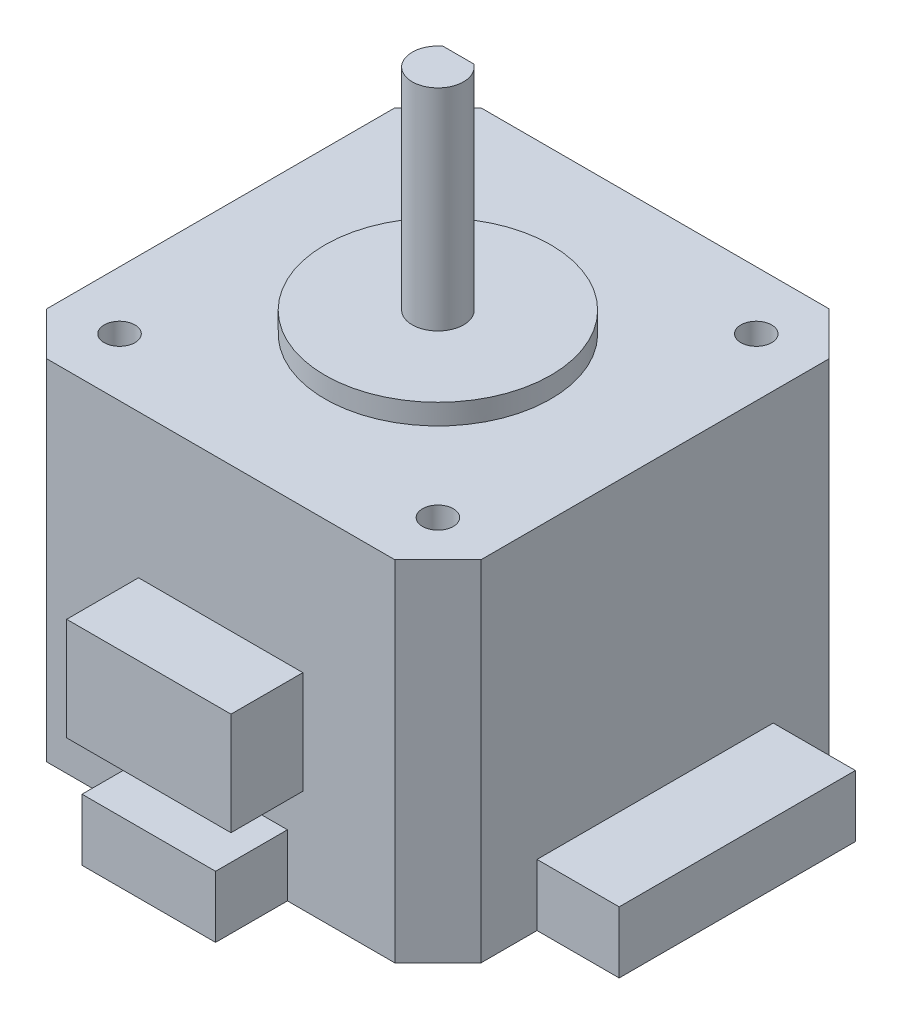
SolidWorks part; units mm, degrees
ref_plane "前视基准面" through (0, 0, 0) normal (0, 0, 1) x (1, 0, 0)
ref_plane "上视基准面" through (0, 0, 0) normal (0, 1, 0) x (1, 0, 0)
ref_plane "右视基准面" through (0, 0, 0) normal (1, 0, 0) x (0, 0, -1)
other "Configuration Table"
sketch "草图1" plane through (0, 0, 0) normal (0, 1, 0) x (1, 0, 0)
  line L1 (0, 0) -> (42.3, 0)
  line L2 (0, 0) -> (0, 42.3)
  line L3 (0, 42.3) -> (42.3, 42.3)
  line L4 (42.3, 0) -> (42.3, 42.3)
  dimension "D1" = 42.3
  dimension "D2" = 42.3
extrude "凸台-拉伸1" add sketch "草图1" along normal blind 34
chamfer "倒角1" distance 4.2 angle 45 4 edges at (0, 17, -42.3) (42.3, 17, -42.3) (0, 17, 0) (42.3, 17, 0)
sketch "草图2" plane through (0, 34, 0) normal (0, 1, 0) x (1, 0, 0)
  line L0 (0, 21.15) -> (42.3, 21.15) construction
  line L1 (0, 38.1) -> (0, 4.2) construction
  line L2 (42.3, 4.2) -> (42.3, 38.1) construction
  line L3 (21.15, 42.3) -> (21.15, 0) construction
  line L4 (38.1, 42.3) -> (4.2, 42.3) construction
  line L5 (4.2, 0) -> (38.1, 0) construction
  circle A0 centre (5.65, 36.65) radius 1.5
  circle A1 centre (36.65, 36.65) radius 1.5
  circle A2 centre (5.65, 5.65) radius 1.5
  circle A3 centre (36.65, 5.65) radius 1.5
  dimension "D1" = 31
  dimension "D2" = 31
  dimension "D3" = 3
extrude "切除-拉伸1" cut sketch "草图2" against normal blind 4.5
sketch "草图3" plane through (0, 34, 0) normal (0, 1, 0) x (1, 0, 0)
  line L0 (0, 21.15) -> (42.3, 21.15) construction
  line L1 (0, 38.1) -> (0, 4.2) construction
  line L2 (42.3, 4.2) -> (42.3, 38.1) construction
  circle A0 centre (21.15, 21.15) radius 11
  point P2 (21.15, 21.15)
  dimension "D1" = 22
extrude "凸台-拉伸2" add sketch "草图3" along normal blind 2
sketch "草图4" plane through (0, 36, 0) normal (0, 1, 0) x (1, 0, 0)
  circle A0 centre (21.15, 21.15) radius 2.5
  dimension "D1" = 5
extrude "凸台-拉伸3" add sketch "草图4" along normal blind 20.5
sketch "草图5" plane through (0, 56.5, 0) normal (0, 1, 0) x (1, 0, 0)
  line L0 (19.65, 23.15) -> (22.65, 23.15)
  circle A0 centre (21.15, 21.15) radius 2.5 construction
  arc A1 (22.65, 23.15) -> (19.65, 23.15) centre (21.15, 21.15) ccw
  dimension "D1" = 2
extrude "切除-拉伸2" cut sketch "草图5" against normal blind 18
sketch "草图6" plane through (0, 0, 0) normal (0, 0, 1) x (1, 0, 0)
  line L0 (21.15, 34) -> (21.15, 0) construction
  line L1 (4.2, 34) -> (38.1, 34) construction
  line L2 (4.2, 0) -> (38.1, 0) construction
  line L4 (13.15, 20) -> (29.15, 20)
  line L5 (13.15, 20) -> (13.15, 10)
  line L6 (13.15, 10) -> (29.15, 10)
  line L7 (29.15, 20) -> (29.15, 10)
  line L8 (14.65, 0) -> (27.65, 0)
  line L9 (14.65, 0) -> (14.65, 6)
  line L10 (14.65, 6) -> (27.65, 6)
  line L11 (27.65, 0) -> (27.65, 6)
  point P10 (0, 0)
  dimension "D1" = 16
  dimension "D2" = 10
  dimension "D3" = 24
  dimension "D4" = 13
  dimension "D5" = 6
extrude "凸台-拉伸4" add sketch "草图6" along normal blind 7
sketch "草图7" plane through (42.3, 0, 0) normal (1, 0, 0) x (0, 0, -1)
  line L0 (4.2, 0) -> (38.1, 0) construction
  line L1 (9.65, 0) -> (32.65, 0)
  line L2 (9.65, 0) -> (9.65, 6)
  line L3 (9.65, 6) -> (32.65, 6)
  line L4 (32.65, 0) -> (32.65, 6)
  line L5 (21.15, 34) -> (21.15, 0) construction
  line L6 (4.2, 34) -> (38.1, 34) construction
  point P10 (0, 0)
  dimension "D1" = 23
  dimension "D2" = 6
extrude "凸台-拉伸5" add sketch "草图7" along normal blind 8
